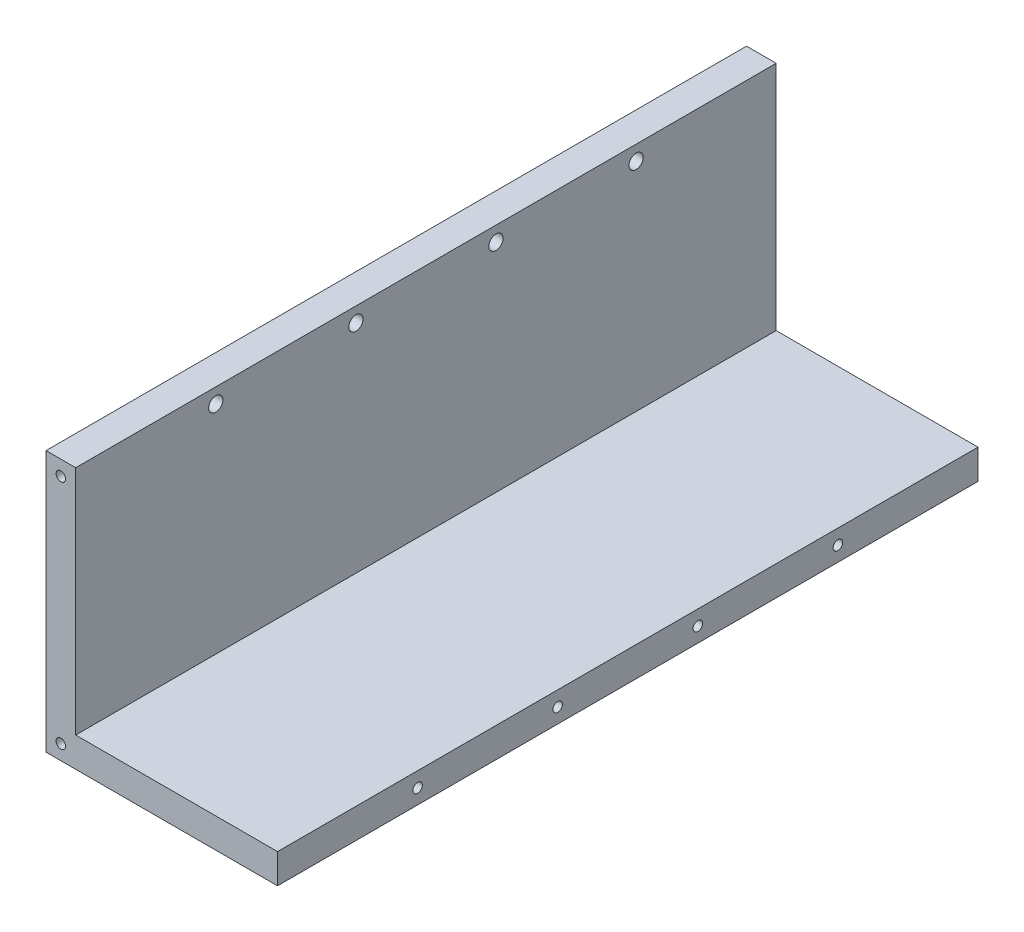
SolidWorks part; units mm, degrees
ref_plane "Plan de face" through (0, 0, 0) normal (1, 0, 0) x (0, 1, 0)
ref_plane "Plan de dessus" through (0, 0, 0) normal (0, 0, 1) x (0, 1, 0)
ref_plane "Plan de droite" through (0, 0, 0) normal (0, 1, 0) x (-1, 0, 0)
sketch "Esquisse1" plane through (0, 0, 0) normal (0, 0, 1) x (0, 1, 0)
  line L0 (0, 0) -> (39, 0)
  line L2 (0, 0) -> (0, -34)
  line L3 (0, -34) -> (-5, -34)
  line L4 (-5, 0) -> (-5, -34)
  line L6 (-5, 0) -> (-5, 5)
  line L7 (-5, 5) -> (39, 5)
  line L8 (39, 0) -> (39, 5)
extrude "Boss_Extrude_Equerre" add sketch "Esquisse1" along normal blind 118
hole_wizard "Fraisage pour vis à tête fraisée M20" positions "Esquisse6" profile "Esquisse3" countersink size "M2" standard "Ansi Metric"
sketch "Esquisse6" plane through (-5, 0, 0) normal (-1, 0, 0) x (0, 0, 1)
  line L2 (118, 39) -> (118, -5) construction
  line L3 (0, 36.5) -> (118, 36.5) construction
  line L4 (0, 39) -> (0, -5) construction
  line L5 (118, -5) -> (0, -5) construction
  point P0 (70.8, 36.5)
  point P2 (94.4, 36.5)
  point P10 (47.2, 36.5)
  point P12 (23.6, 36.5)
  dimension "D5" = 23.6
  dimension "D6" = 23.6
  dimension "D1" = 23.6
sketch "Esquisse3" plane through (-5, 36.5, 70.8) normal (0, 1, 0) x (0, 0, 1)
  line L0 (0, 0) -> (0, 5.721)
  line L1 (0, 5.721) -> (1.2, 5)
  line L2 (1.2, 5) -> (1.2, 1)
  line L3 (1.2, 1) -> (2.2, 0)
  line L5 (2.2, 0) -> (0, 0)
  line L6 (-1.2, 1) -> (-2.2, 0) construction
  line L10 (0, 5.721) -> (-1.2, 5) construction
  line L11 (0, -6.35) -> (0, 107.95) construction
  dimension "Diamètre du perçage" = 2.4
  dimension "Profondeur du perçage" = 5
  dimension "Diamètre du fraisage entrant" = 4.4
  dimension "Angle du fraisage entrant" = 90
  dimension "Angle de pointe" = 118
hole_wizard "Trou taraudé M2x0.43" positions "Esquisse7" profile "Esquisse8" tap size "M2x0.4" standard "Ansi Metric"
sketch "Esquisse7" plane through (34, 0, 0) normal (1, 0, 0) x (0, 1, 0)
  line L1 (-5, 0) -> (0, 0) construction
  line L4 (-2.5, 0) -> (-2.5, 118) construction
  line L5 (-5, 118) -> (0, 118) construction
  point P0 (-2.5, 70.8)
  point P2 (-2.5, 94.4)
  point P13 (-2.5, 47.2)
  point P15 (-2.5, 23.6)
  dimension "D5" = 23.6
  dimension "D1" = 23.6
  dimension "D3" = 23.6
  dimension "D4" = 23.6
cosmetic thread "Filetage de perçage1"
cosmetic thread "Filetage de perçage2"
cosmetic thread "Filetage de perçage3"
cosmetic thread "Filetage de perçage4"
sketch "Esquisse8" plane through (34, -2.5, 70.8) normal (0, 1, 0) x (0, 0, -1)
  line L0 (0, 0) -> (0, 8.4807)
  line L1 (0, 8.4807) -> (0.8, 8)
  line L2 (0.8, 8) -> (0.8, 0)
  line L5 (0.8, 0) -> (0, 0)
  line L10 (0, 8.4807) -> (-0.8, 8) construction
  line L11 (0, -6.35) -> (0, 107.95) construction
  dimension "Diamètre du trou pour taraudage" = 1.6
  dimension "Profondeur du trou pour taraudage" = 8
  dimension "Angle de pointe" = 118
hole_wizard "Trou taraudé M2x0.44" positions "Esquisse9" profile "Esquisse11" tap size "M2x0.4" standard "Ansi Metric"
sketch "Esquisse9" plane through (0, 0, 118) normal (0, 0, 1) x (1, 0, 0)
  line L0 (-2.5, 39) -> (-2.5, -5) construction
  line L1 (0, 39) -> (-5, 39) construction
  line L2 (-5, -5) -> (34, -5) construction
  line L3 (0, 36.5) -> (-7.2751, 36.5) construction
  line L4 (0, 0) -> (0, 39) construction
  line L12 (-5, -2.5) -> (34, -2.5) construction
  line L13 (-5, 39) -> (-5, -5) construction
  line L14 (34, -5) -> (34, 0) construction
  point P0 (-2.5, 36.5)
  point P2 (-2.5, -2.5)
  dimension "D1" = 2.5
cosmetic thread "Filetage de perçage6"
cosmetic thread "Filetage de perçage7"
sketch "Esquisse11" plane through (-2.5, 36.5, 118) normal (1, 0, 0) x (0, -1, 0)
  line L0 (0, 0) -> (0, 8.4807)
  line L1 (0, 8.4807) -> (0.8, 8)
  line L2 (0.8, 8) -> (0.8, 0)
  line L5 (0.8, 0) -> (0, 0)
  line L10 (0, 8.4807) -> (-0.8, 8) construction
  line L11 (0, -6.35) -> (0, 107.95) construction
  dimension "Diamètre du trou pour taraudage" = 1.6
  dimension "Profondeur du trou pour taraudage" = 8
  dimension "Angle de pointe" = 118
ref_plane "Plan1" through (0, 0, 59) normal (0, 0, 1) x (1, 0, 0)
mirror "Symétrie1" about plane through (0, 0, 59) normal (0, 0, 1) of "Trou taraudé M2x0.44"
cosmetic thread "Filetage de perçage8"
cosmetic thread "Filetage de perçage9"
equation "\"Plaque_L\" =\"Cavite_L\"+\"Cavite_E\"'longueur plaque"
equation "\"Plaque_H\" = \"Cavite_L\"+\"Cavite_E\"'largeur plaque"
equation "\"Plaque_E\"= 2mm'épaisseur plaque"
equation "\"Trou_R\"= 1.2mm'rayon perforation base"
equation "\"Trou_dx\"= 4mm'distance entre trou sur x"
equation "\"Trou-dy\"= 4mm'distance entre trou sur y"
equation "\"Cavite_H\" = 22mm'hauteur cavité"
equation "\"Cavite_L\" =\"Cavite_largeur\"+\"Cavite_E\"'longueur cavité"
equation "\"Cavite_E\"= 3mm'épaisseur cavité"
equation "\"Offset_Z\"= 0mm"
equation "\"D2@Esquisse1\"=\"Enveloppe_E\""
equation "\"D3@Esquisse1\"=\"Longueur_equerre_enveloppe\""
equation "\"D1@Esquisse1\"=\"Largeur_equerre_enveloppe\""
equation "\"Vis_Diam\"= 1.6mm"
equation "\"Offset_Bord\"= \"Cavite_E\" / 2"
equation "\"Vis_Long\"= 5mm"
equation "\"Perc_Passage\"= 1.8mm"
equation "\"Perc_Taraud\"= 1.3mm"
equation "\"Fraisure_Diam\"= 3mm"
equation "\"Fraisure_Prof\"= 1mm"
equation "\"Offset_hauteur_vis1\"= \"Cavite_E\""
equation "\"Offset_hauteur_vis2\"= \"Cavite_H\" - \"Cavite_E\""
equation "\"Perc_Profondeur\"= 8mm"
equation "\"Taraud_Profondeur\"= \"Cavite_E\""
equation "\"Cavite_largeur\"= 28mm'largeur cavité"
equation "\"D1@Boss_Extrude_Equerre\"=\"H_total\""
equation "\"H_total\"=118mm'122-2*2"
equation "\"espace_trou\"= 22.6mm"
equation "\"D5@Esquisse6\"=\"espace_vis\""
equation "\"D6@Esquisse6\"=\"espace_vis\""
equation "\"D2@Esquisse6\"=\"espace_vis\""
equation "\"D3@Esquisse7\"=\"espace_vis\""
equation "\"D4@Esquisse7\"=\"espace_vis\""
equation "\"D5@Esquisse7\"=\"espace_vis\""
equation "\"D1@Esquisse9\"=\"Offset_Enveloppe\""
equation "\"D2@Esquisse9\"=\"Offset_Enveloppe\""
equation "\"espace_vis\"=23.6mm'"
equation "\"Enveloppe_E\"=5mm"
equation "\"Offset_cavite\" = \"Cavite_E\" / 2"
equation "\"Offset_Enveloppe\" = \"Enveloppe_E\" / 2"
equation "\"D3@Esquisse6\"=\"Longueur_equerre_enveloppe\"+\"Enveloppe_E\"-\"Offset_Enveloppe\""
equation "\"Largeur_enveloppe\"=\"Cavite_largeur\"+\"Cavite_E\""
equation "\"Longueur_enveloppe\"=\"Cavite_L\"+\"Enveloppe_E\""
equation "\"N_Plaque\" = 7"
equation "\"N_Cavite\"= 6"
equation "\"Largeur_equerre_enveloppe\"=\"Cavite_L\"+\"Cavite_E\""
equation "\"Longueur_equerre_enveloppe\"=\"Cavite_L\"+\"Cavite_E\"+\"Enveloppe_E\""
equation "\"largeur_plaque_enveloppe\"=\"Longueur_equerre_enveloppe\"+\"Enveloppe_E\""
equation "\"D1@Esquisse6\"=\"espace_vis\""
equation "\"D1@Esquisse7\"=\"espace_vis\""
